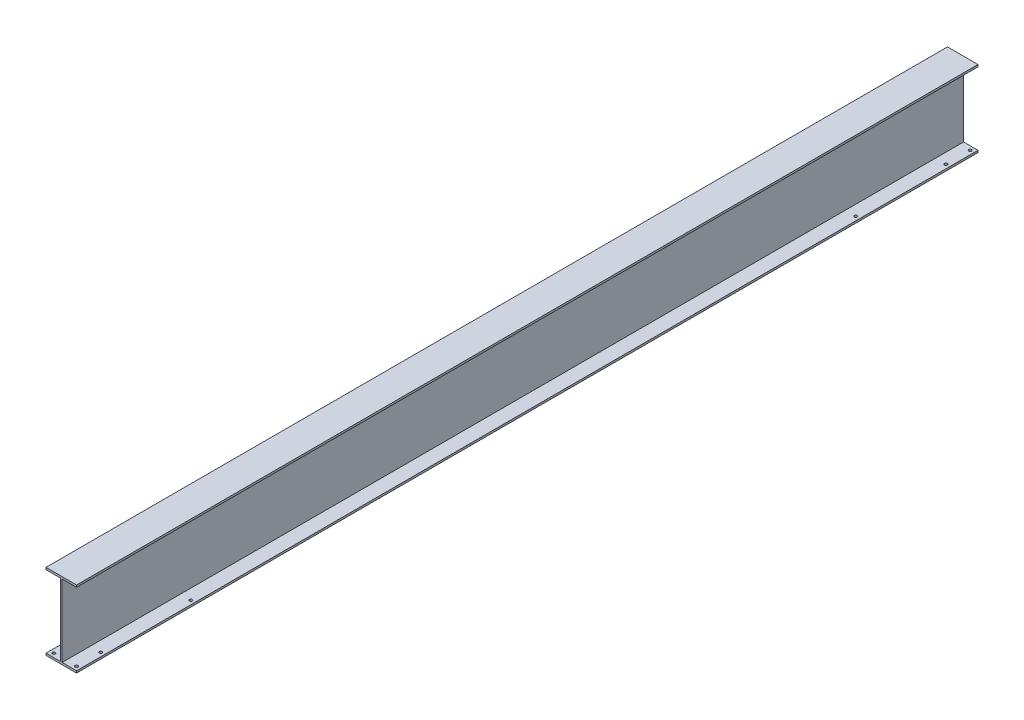
SolidWorks part; units mm, degrees
ref_plane "Alzado" through (0, 0, 0) normal (0, 0, 1) x (1, 0, 0)
ref_plane "Planta" through (0, 0, 0) normal (0, 1, 0) x (1, 0, 0)
ref_plane "Vista lateral" through (0, 0, 0) normal (1, 0, 0) x (0, 0, -1)
sketch "Croquis1" plane through (0, 0, 0) normal (0, 0, 1) x (1, 0, 0)
  line L0 (0, 0) -> (101.6, 0)
  line L1 (0, 0) -> (0, -6.8)
  line L2 (0, -6.8) -> (47.9, -6.8)
  line L3 (50.8, 0) -> (50.8, -254) construction
  line L4 (47.9, -6.8) -> (47.9, -247.2)
  line L5 (47.9, -247.2) -> (0, -247.2)
  line L6 (0, -247.2) -> (0, -254)
  line L7 (0, -254) -> (101.6, -254)
  line L8 (101.6, -247.2) -> (101.6, -254)
  line L9 (53.7, -247.2) -> (101.6, -247.2)
  line L10 (53.7, -6.8) -> (53.7, -247.2)
  line L11 (101.6, -6.8) -> (53.7, -6.8)
  line L12 (101.6, 0) -> (101.6, -6.8)
  dimension "D1" = 50.8
  dimension "D2" = 6.8
  dimension "D3" = 254
  dimension "D4" = 2.9
  dimension "D5" = 6.8
extrude "Saliente-Extruir1" add sketch "Croquis1" along normal blind 3000
sketch "Croquis2" plane through (0, -254, 0) normal (0, -1, 0) x (1, 0, 0)
  line L0 (50.8, 3000) -> (50.8, 2987) construction
  line L1 (0, 3000) -> (101.6, 3000) construction
  line L2 (50.8, 2987) -> (88.6, 2987) construction
  line L3 (88.6, 2987) -> (88.6, 2906.61) construction
  line L4 (13, 2987) -> (13, 2906.61) construction
  line L5 (101.6, 1500) -> (0, 1500) construction
  line L6 (101.6, 3000) -> (101.6, 0) construction
  line L7 (0, 3000) -> (0, 0) construction
  line L8 (13, 13) -> (13, 93.39) construction
  line L9 (88.6, 13) -> (88.6, 93.39) construction
  line L10 (50.8, 13) -> (88.6, 13) construction
  line L11 (50.8, 0) -> (50.8, 13) construction
  line L12 (88.6, 2906.61) -> (88.6, 2606.6) construction
  circle A0 centre (88.6, 2987) radius 4.7625
  circle A1 centre (88.6, 2906.61) radius 4.7625
  circle A2 centre (13, 2906.61) radius 4.7625
  circle A3 centre (13, 2987) radius 4.7625
  circle A4 centre (13, 13) radius 4.7625
  circle A5 centre (13, 93.39) radius 4.7625
  circle A6 centre (88.6, 93.39) radius 4.7625
  circle A7 centre (88.6, 13) radius 4.7625
  circle A8 centre (88.6, 2606.6) radius 4.7625
  circle A9 centre (13, 2606.6) radius 4.7625
  circle A10 centre (13, 393.4) radius 4.7625
  circle A11 centre (88.6, 393.4) radius 4.7625
  dimension "D2" = 9.525
  dimension "D4" = 9.525
  dimension "D7" = 9.525
  dimension "D1" = 13
  dimension "D3" = 37.8
  dimension "D5" = 80.39
  dimension "D6" = 380.4
extrude "Cortar-Extruir1" cut sketch "Croquis2" against normal up to surface (6.8 mm away) up to face at (77.65, -247.2, 1500)
